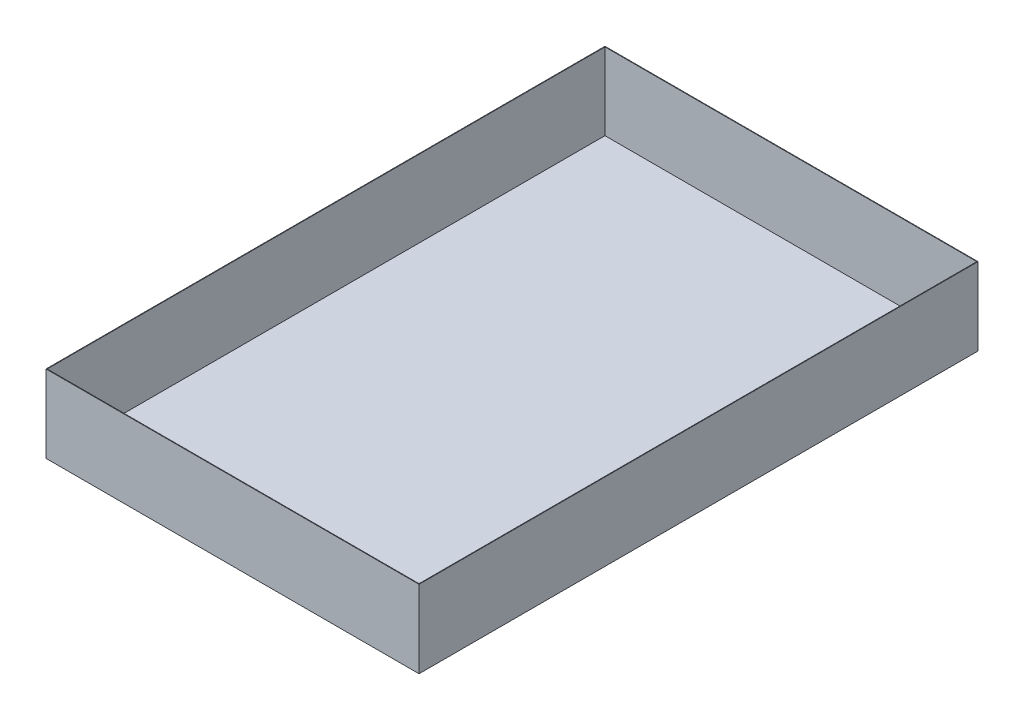
SolidWorks part; units mm, degrees
ref_plane "Front Plane" through (0, 0, 0) normal (0, 0, 1) x (1, 0, 0)
ref_plane "Top Plane" through (0, 0, 0) normal (0, 1, 0) x (1, 0, 0)
ref_plane "Right Plane" through (0, 0, 0) normal (1, 0, 0) x (0, 0, -1)
sketch "Sketch1" plane through (0, 0, 0) normal (0, 1, 0) x (1, 0, 0)
  line L1 (-240.75, 360.75) -> (240.75, 360.75)
  line L2 (-240.75, 360.75) -> (-240.75, -360.75)
  line L3 (-240.75, -360.75) -> (240.75, -360.75)
  line L4 (240.75, 360.75) -> (240.75, -360.75)
  line L5 (-240.75, 360.75) -> (240.75, -360.75) construction
  line L6 (-240.75, -360.75) -> (240.75, 360.75) construction
  point P0 (0, 0)
  dimension "D1" = 721.5
  dimension "D2" = 481.5
extrude "Boss-Extrude1" add sketch "Sketch1" along normal blind 100
shell "Shell1" thickness 0.75
sketch "Sketch2" plane through (0, 0.75, 0) normal (0, 1, 0) x (1, 0, 0)
  line L1 (-240.75, -360.75) -> (240.75, -360.75) construction
  line L3 (240.75, -360.75) -> (240.75, 360.75) construction
  circle A0 centre (120.75, -310.75) radius 13.5
  dimension "D1" = 50
  dimension "48" = 27
  dimension "D2" = 120
extrude "Cut-Extrude1" cut sketch "Sketch2" against normal blind 10
